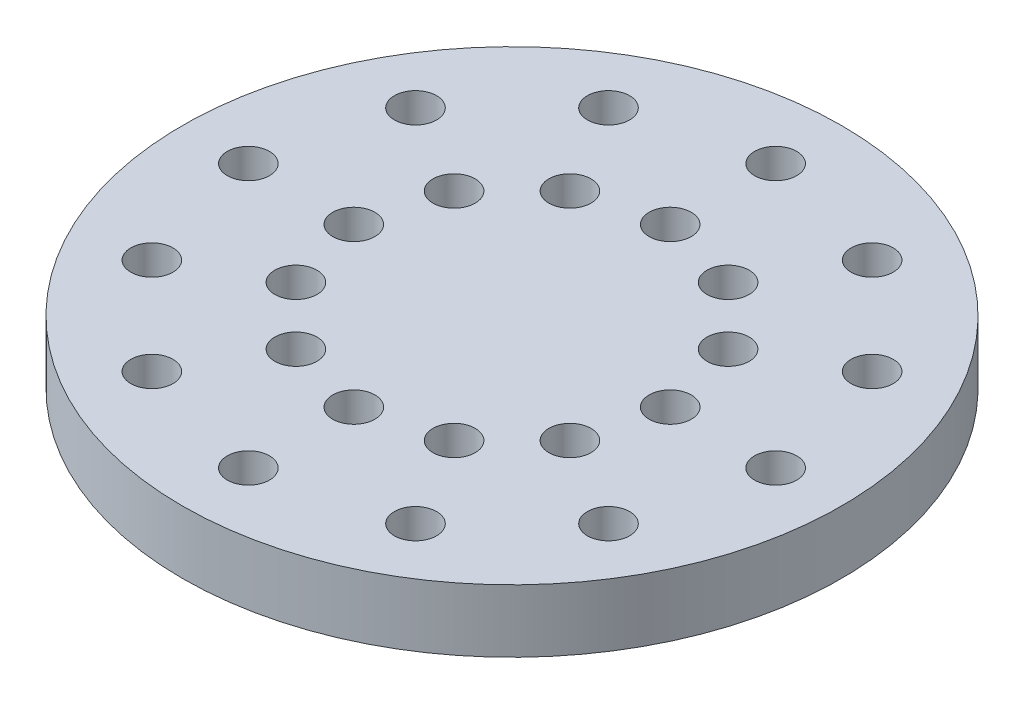
SolidWorks part; units mm, degrees
ref_plane "Front Plane" through (0, 0, 0) normal (0, 0, 1) x (1, 0, 0)
ref_plane "Top Plane" through (0, 0, 0) normal (0, 1, 0) x (1, 0, 0)
ref_plane "Right Plane" through (0, 0, 0) normal (1, 0, 0) x (0, 0, -1)
sketch "Sketch1" plane through (0, 0, 0) normal (0, 1, 0) x (1, 0, 0)
  line L0 (0, 0) -> (20, 0) construction
  circle A0 centre (0, 0) radius 25
  circle A1 centre (20, 0) radius 1.6
  circle A2 centre (12, 0) radius 1.6
  circle A3 centre (17.3205, -10) radius 1.6
  circle A4 centre (10.3923, -6) radius 1.6
  circle A5 centre (10, -17.3205) radius 1.6
  circle A6 centre (6, -10.3923) radius 1.6
  circle A7 centre (0, -20) radius 1.6
  circle A8 centre (0, -12) radius 1.6
  circle A9 centre (-10, -17.3205) radius 1.6
  circle A10 centre (-6, -10.3923) radius 1.6
  circle A11 centre (-17.3205, -10) radius 1.6
  circle A12 centre (-10.3923, -6) radius 1.6
  circle A13 centre (-20, 0) radius 1.6
  circle A14 centre (-12, 0) radius 1.6
  circle A15 centre (-17.3205, 10) radius 1.6
  circle A16 centre (-10.3923, 6) radius 1.6
  circle A17 centre (-10, 17.3205) radius 1.6
  circle A18 centre (-6, 10.3923) radius 1.6
  circle A19 centre (0, 20) radius 1.6
  circle A20 centre (0, 12) radius 1.6
  circle A21 centre (10, 17.3205) radius 1.6
  circle A22 centre (6, 10.3923) radius 1.6
  circle A23 centre (17.3205, 10) radius 1.6
  circle A24 centre (10.3923, 6) radius 1.6
  point P54 (0, 0)
  dimension "D1" = 50
  dimension "D2" = 3.2
  dimension "D3" = 20
  dimension "D4" = 8
  dimension "D5" = 12
extrude "Boss-Extrude1" add sketch "Sketch1" along normal blind 4.7625
